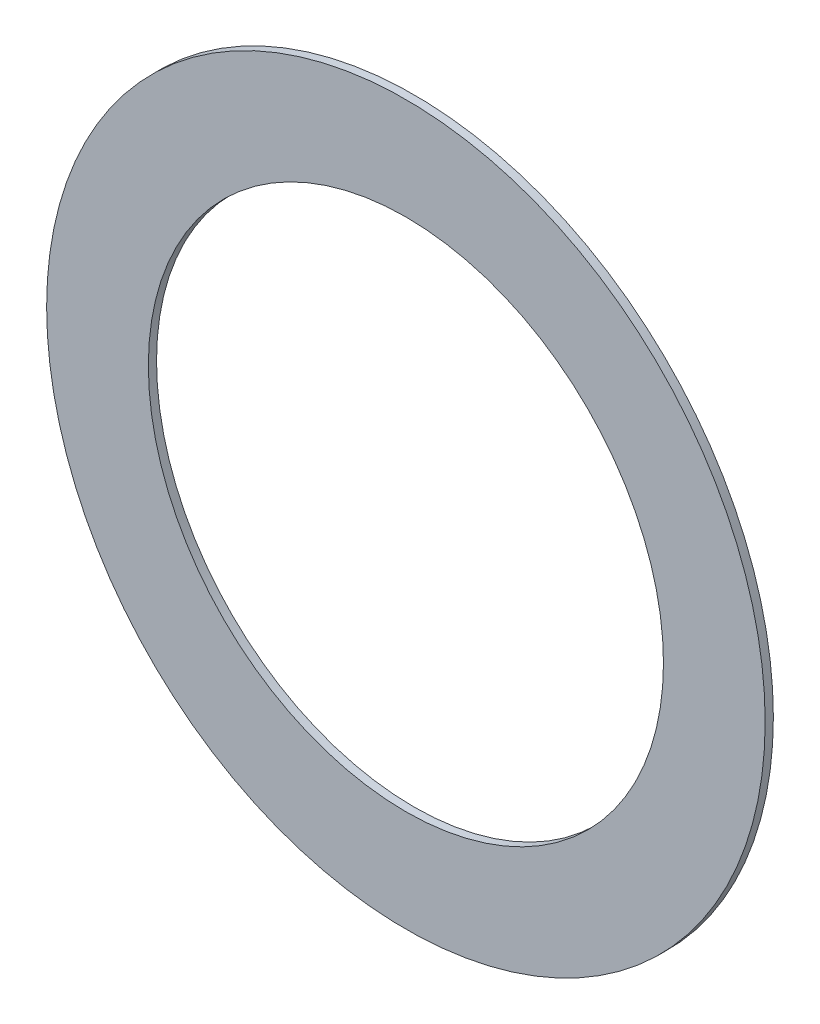
SolidWorks part; units mm, degrees
material "AISI 316 Stainless Steel Sheet (SS)"
ref_plane "Front Plane" through (0, 0, 0) normal (0, 0, 1) x (1, 0, 0)
ref_plane "Top Plane" through (0, 0, 0) normal (0, 1, 0) x (1, 0, 0)
ref_plane "Right Plane" through (0, 0, 0) normal (1, 0, 0) x (0, 0, -1)
sketch "Sketch1" plane through (0, 0, 0) normal (0, 0, 1) x (1, 0, 0)
  circle A0 centre (0, 0) radius 3.9878
  circle A1 centre (0, 0) radius 5.5626
  dimension "D1" = 7.9756
  dimension "D2" = 11.1252
extrude "Boss-Extrude1" add sketch "Sketch1" along normal blind 0.127
